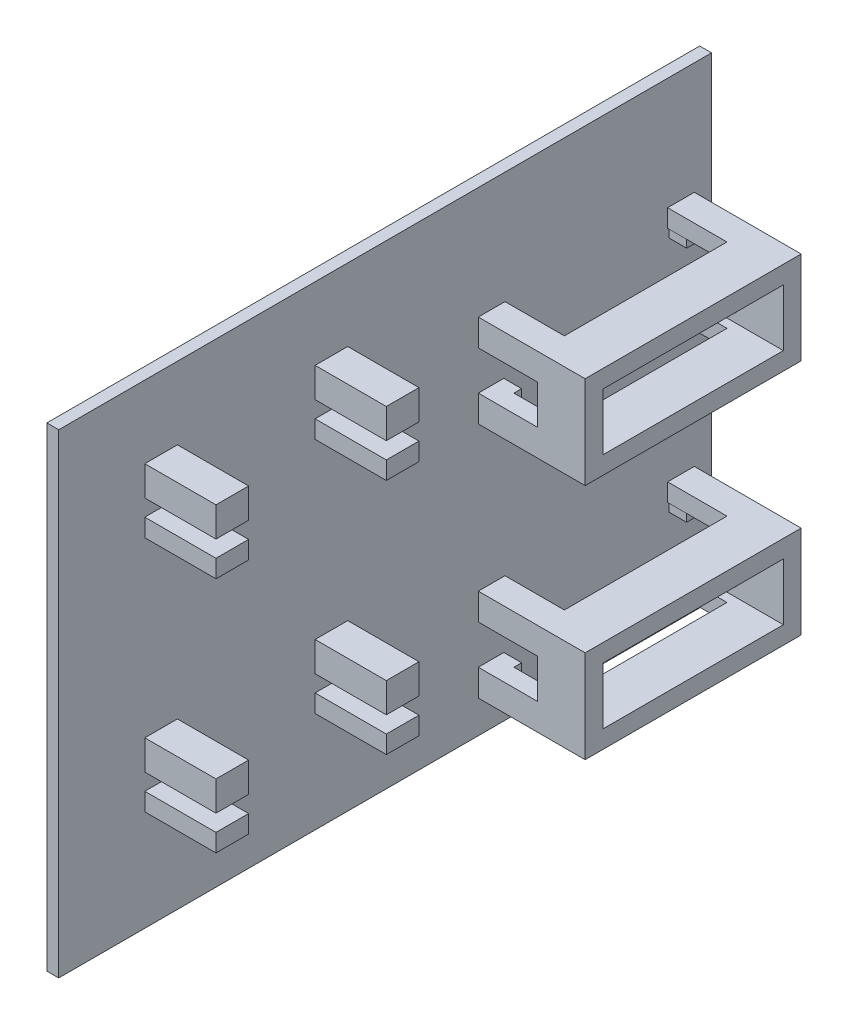
SolidWorks part; units mm, degrees
ref_plane "前视基准面" through (0, 0, 0) normal (0, 0, 1) x (1, 0, 0)
ref_plane "上视基准面" through (0, 0, 0) normal (0, 1, 0) x (1, 0, 0)
ref_plane "右视基准面" through (0, 0, 0) normal (1, 0, 0) x (0, 0, -1)
sketch "草图1" plane through (0, 0, 0) normal (1, 0, 0) x (0, 0, -1)
  line L1 (-70, -40) -> (70, -40)
  line L2 (-70, -40) -> (-70, 40)
  line L3 (-70, 40) -> (70, 40)
  line L4 (70, -40) -> (70, 40)
  line L5 (-70, -40) -> (70, 40) construction
  line L6 (-70, 40) -> (70, -40) construction
  point P0 (0, 0)
  dimension "D1" = 80
  dimension "D2" = 140
extrude "凸台-拉伸1" add sketch "草图1" along normal blind 2
sketch "草图2" plane through (2, 0, 0) normal (1, 0, 0) x (0, 0, -1)
  line L0 (-26.8, -17.2) -> (-21.3, -17.2)
  line L1 (-21.3, -17.2) -> (-21.3, -12.2)
  line L2 (-50, -17.2) -> (-50, -12.2)
  line L4 (-26.8, -17.2) -> (-26.8, -12.2)
  line L5 (-21.3, -23) -> (-21.3, -20)
  line L6 (-50, 17) -> (-55.5, 17)
  line L7 (-55.5, 20) -> (-50, 20)
  line L8 (-26.8, 22.8) -> (-21.3, 22.8)
  line L9 (-21.3, -12.2) -> (-26.8, -12.2)
  line L10 (-70, 40) -> (-70, -40) construction
  line L11 (-50, -17.2) -> (-55.5, -17.2)
  line L12 (-26.8, -20) -> (-26.8, -23)
  line L13 (-26.8, -23) -> (-21.3, -23)
  line L15 (-55.5, -17.2) -> (-55.5, -12.2)
  line L17 (-50, -20) -> (-50, -23)
  line L18 (-50, -23) -> (-55.5, -23)
  line L19 (-55.5, -23) -> (-55.5, -20)
  line L20 (-55.5, -20) -> (-50, -20)
  line L21 (-26.8, -20) -> (-21.3, -20)
  line L22 (-55.5, -12.2) -> (-50, -12.2)
  line L23 (-26.8, 17) -> (-21.3, 17)
  line L24 (-21.3, 17) -> (-21.3, 20)
  line L25 (-55.5, 17) -> (-55.5, 20)
  line L26 (-26.8, 20) -> (-26.8, 17)
  line L27 (-55.5, 22.8) -> (-55.5, 27.8)
  line L28 (-55.5, 27.8) -> (-50, 27.8)
  line L29 (-21.3, 27.8) -> (-26.8, 27.8)
  line L30 (-21.3, 22.8) -> (-21.3, 27.8)
  line L31 (-50, 20) -> (-50, 17)
  line L32 (-26.8, 22.8) -> (-26.8, 27.8)
  line L34 (-26.8, 20) -> (-21.3, 20)
  line L35 (-50, 22.8) -> (-50, 27.8)
  line L36 (-50, 22.8) -> (-55.5, 22.8)
  point P28 (-135, -22.5)
  point P31 (135, -22.5)
  point P32 (-135, 22.5)
  point P34 (135, 22.5)
  dimension "D14" = 20
  dimension "D1" = 5.5
  dimension "D2" = 5.5
  dimension "D3" = 5.5
  dimension "D4" = 3
  dimension "D5" = 40
  dimension "D6" = 20
  dimension "D7" = 5.5
  dimension "D8" = 2.8
  dimension "D9" = 23.2
  dimension "D10" = 3
  dimension "D11" = 5
  dimension "D12" = 5
  dimension "D13" = 23.2
  dimension "D15" = 2.8
  dimension "D16" = 5
  dimension "D17" = 3
  dimension "D18" = 5
  dimension "D19" = 3
  dimension "D20" = 5.5
  dimension "D21" = 5.5
  dimension "D22" = 23.2
  dimension "D23" = 5.5
  dimension "D24" = 5.5
extrude "凸台-拉伸2" add sketch "草图2" along normal blind 12
sketch "草图3" plane through (2, 0, 0) normal (1, 0, 0) x (0, 0, -1)
  line L0 (70, 40) -> (-70, 40) construction
  line L1 (70, -40) -> (40, -40)
  line L2 (70, -40) -> (70, 40)
  line L3 (70, 40) -> (40, 40)
  line L4 (40, -40) -> (40, 40)
  dimension "D1" = 30
extrude "切除-拉伸1" cut sketch "草图3" against normal blind 3
sketch "草图4" plane through (2, 0, 0) normal (1, 0, 0) x (0, 0, -1)
  line L1 (3.7, -31.5) -> (34.1, -31.5)
  line L2 (3.7, -31.5) -> (3.7, -21.9)
  line L3 (3.7, -21.9) -> (34.1, -21.9)
  line L4 (34.1, -31.5) -> (34.1, -21.9)
  line L5 (3.7, -31.5) -> (34.1, -21.9) construction
  line L6 (3.7, -21.9) -> (34.1, -31.5) construction
  line L7 (0.7, -18.9) -> (37.1, -18.9)
  line L8 (37.1, -34.5) -> (37.1, -18.9)
  line L9 (0.7, -34.5) -> (37.1, -34.5)
  line L10 (0.7, -34.5) -> (0.7, -18.9)
  line L11 (-21.3, -20) -> (-26.8, -20) construction
  line L12 (-21.3, -23) -> (-21.3, -20) construction
  point P0 (18.9, -26.7)
  point P5 (18.9, -26.7)
  dimension "D1" = 30.4
  dimension "D2" = 9.6
  dimension "D3" = 22
  dimension "D4" = 3
  dimension "D5" = 11.5
extrude "凸台-拉伸3" add sketch "草图4" along normal blind 18
sketch "草图5" plane through (0, -34.5, 0) normal (0, -1, 0) x (1, 0, 0)
  line L0 (12, -5.2) -> (2, -5.2)
  line L3 (2, -0.7) -> (2, -37.1) construction
  line L6 (2, -5.2) -> (2, -32.6)
  line L7 (2, -32.6) -> (12, -32.6)
  line L8 (20, -0.7) -> (2, -0.7) construction
  line L9 (20, -37.1) -> (2, -37.1) construction
  line L10 (12, -32.6) -> (12, -5.2)
  dimension "D1" = 4.5
  dimension "D2" = 4.5
extrude "切除-拉伸2" cut sketch "草图5" against normal blind 20
sketch "草图6" plane through (2, 0, 0) normal (1, 0, 0) x (0, 0, -1)
  line L0 (3.7, -31.5) -> (34.1, -31.5) construction
  line L1 (3.7, -21.9) -> (5, -21.9)
  line L2 (3.7, -21.9) -> (3.7, -31.5)
  line L3 (3.7, -31.5) -> (5, -31.5)
  line L4 (5, -21.9) -> (5, -31.5)
  line L5 (32.6, -31.5) -> (34.1, -31.5) construction
  line L6 (34.1, -21.9) -> (32.8, -21.9)
  line L7 (34.1, -21.9) -> (34.1, -31.5)
  line L8 (34.1, -31.5) -> (32.8, -31.5)
  line L9 (32.8, -21.9) -> (32.8, -31.5)
  dimension "D1" = 1.3
  dimension "D2" = 1.3
extrude "凸台-拉伸4" add sketch "草图6" along normal blind 3
sketch "草图8" plane through (0, 0, -37.1) normal (0, 0, -1) x (-1, 0, 0)
  line L0 (-2, -34.5) -> (-2, -18.9) construction
  line L1 (-2, -30) -> (-12, -30)
  line L2 (-2, -30) -> (-2, -23.4)
  line L3 (-2, -23.4) -> (-12, -23.4)
  line L4 (-12, -30) -> (-12, -23.4)
  line L5 (-20, -18.9) -> (-2, -18.9) construction
  line L6 (-20, -34.5) -> (-2, -34.5) construction
  dimension "D1" = 4.5
  dimension "D2" = 4.5
  dimension "D3" = 10
extrude "切除-拉伸3" cut sketch "草图8" against normal blind 40
pattern_linear "阵列(线性)1" count 2 spacing 40 along (0, 1, 0) of "凸台-拉伸3", "切除-拉伸2", "切除-拉伸3", "凸台-拉伸4"
